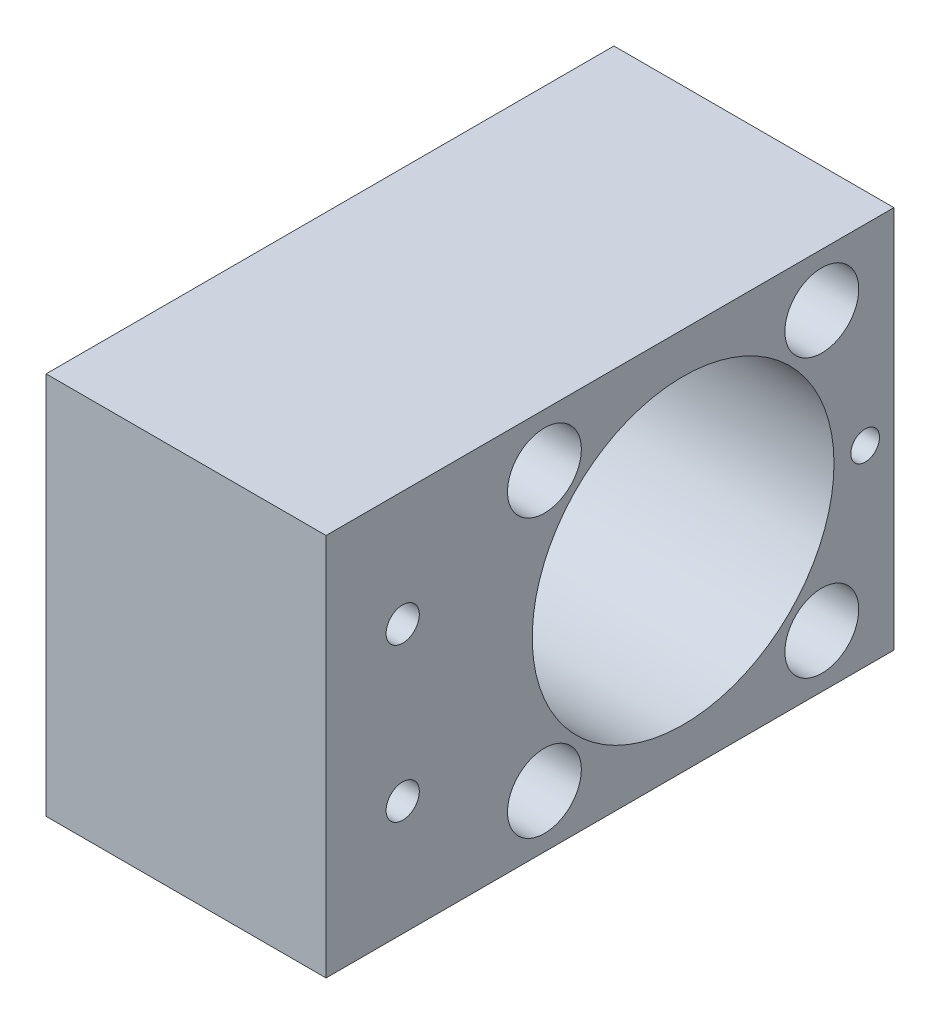
SolidWorks part; units mm, degrees
other "Markup1"
sketch "Sketch12" plane through (-25.617, 333.1179, 201.2722) normal (-0.6084, 0.5079, -0.6099) x (-0.708, 0, 0.7062)
other "Markup2"
sketch "Sketch13" plane through (-25.617, 333.1179, 201.2722) normal (-0.6084, 0.5079, -0.6099) x (-0.708, 0, 0.7062)
material "Delrin 2700 NC010, Low Viscosity Acetal Copolymer (SS)"
ref_plane "Front Plane" through (0, 0, 0) normal (0, 0, 1) x (1, 0, 0)
ref_plane "Top Plane" through (0, 0, 0) normal (0, 1, 0) x (1, 0, 0)
ref_plane "Right Plane" through (0, 0, 0) normal (1, 0, 0) x (0, 0, -1)
sketch "Sketch1" plane through (20.7701, 0, 0) normal (-1, 0, 0) x (0, 0, 1)
  line L0 (201.2722, 94.9929) -> (201.2722, 393.4429) construction
  line L1 (295.3601, 333.1179) -> (201.2722, 333.1179)
  line L2 (295.3601, 333.1179) -> (295.3601, 269.6179)
  line L3 (295.3601, 269.6179) -> (201.2722, 269.6179)
  line L4 (201.2722, 333.1179) -> (201.2722, 269.6179)
  line L5 (255.2472, 301.3679) -> (310.0729, 301.3679) construction
  line L6 (282.6601, 314.0679) -> (282.6601, 288.6679) construction
  circle A9 centre (236.1972, 301.3679) radius 25
  arc A11 (261.1972, 301.3679) -> (211.1972, 301.3679) centre (236.1972, 301.3679) ccw construction
  point P6 (295.3601, 301.3679)
  point P16 (282.6601, 314.0679)
  point P17 (282.6601, 288.6679)
  dimension "D1" = 63.5
  dimension "D2" = 12.7
extrude "Boss-Extrude1" add sketch "Sketch1" along normal up to surface (46.3871 mm away) from surface at 0
hole_wizard "CBORE for M5 Hex Head Bolt1" positions "Sketch3" profile "Sketch5" counterbore size "M5" standard "ANSI Metric" end condition through all
sketch "Sketch3" plane through (20.7701, 0, 0) normal (1, 0, 0) x (0, 0, -1)
  point P0 (-259.1782, 324.3489)
  point P3 (-259.1782, 278.3869)
  point P6 (-213.2162, 278.3869)
  point P9 (-213.2162, 324.3489)
sketch "Sketch5" plane through (20.7701, 324.3489, 259.1782) normal (0, 1, 0) x (0, 0, -1)
  line L0 (0, 0) -> (0, 46.3871)
  line L1 (0, 46.3871) -> (2.75, 46.3871)
  line L3 (2.75, 46.3871) -> (2.75, 10)
  line L4 (2.75, 10) -> (6.12, 10)
  line L5 (6.12, 10) -> (6.12, 0)
  line L7 (6.12, 0) -> (0, 0)
  line L11 (0, -6.35) -> (0, 107.95) construction
  dimension "Thru Hole Dia." = 5.5
  dimension "Thru Hole Depth" = 46.3871
  dimension "C'Bore Dia." = 12.24
  dimension "C'Bore Depth" = 10
hole_wizard "CBORE for M5 Hex Head Bolt2" positions "Sketch8" profile "Sketch9" counterbore size "M5" standard "ANSI Metric" end condition through all
sketch "Sketch8" plane through (-25.617, 0, 0) normal (-1, 0, 0) x (0, 0, 1)
  point P0 (282.6601, 314.0679)
  point P3 (282.6601, 288.6679)
sketch "Sketch9" plane through (-25.617, 314.0679, 282.6601) normal (0, 1, 0) x (0, 0, 1)
  line L0 (0, 0) -> (0, 46.3871)
  line L1 (0, 46.3871) -> (2.75, 46.3871)
  line L3 (2.75, 46.3871) -> (2.75, 10)
  line L4 (2.75, 10) -> (6.12, 10)
  line L5 (6.12, 10) -> (6.12, 0)
  line L7 (6.12, 0) -> (0, 0)
  line L11 (0, -6.35) -> (0, 107.95) construction
  dimension "Thru Hole Dia." = 5.5
  dimension "Thru Hole Depth" = 46.3871
  dimension "C'Bore Dia." = 12.24
  dimension "C'Bore Depth" = 10
hole_wizard "Hole for #6 300® SC Nuts (SP)1" positions "Sketch10" profile "Sketch11" hole size "#6-32" standard "PEM® Inch"
sketch "Sketch10" plane through (20.7701, 0, 0) normal (1, 0, 0) x (0, 0, -1)
  point P0 (-206.0347, 301.3679)
  point P4 (0, 0)
sketch "Sketch11" plane through (20.7701, 301.3679, 206.0347) normal (0, 1, 0) x (0, 0, -1)
  line L0 (0, 0) -> (0, 14.1308)
  line L1 (0, 14.1308) -> (2.3812, 12.7)
  line L2 (2.3812, 12.7) -> (2.3812, 0)
  line L5 (2.3812, 0) -> (0, 0)
  line L10 (0, 14.1308) -> (-2.3813, 12.7) construction
  line L11 (0, -6.35) -> (0, 107.95) construction
  dimension "Hole Dia." = 4.7625
  dimension "Hole Depth" = 12.7
  dimension "Drill Angle" = 118
